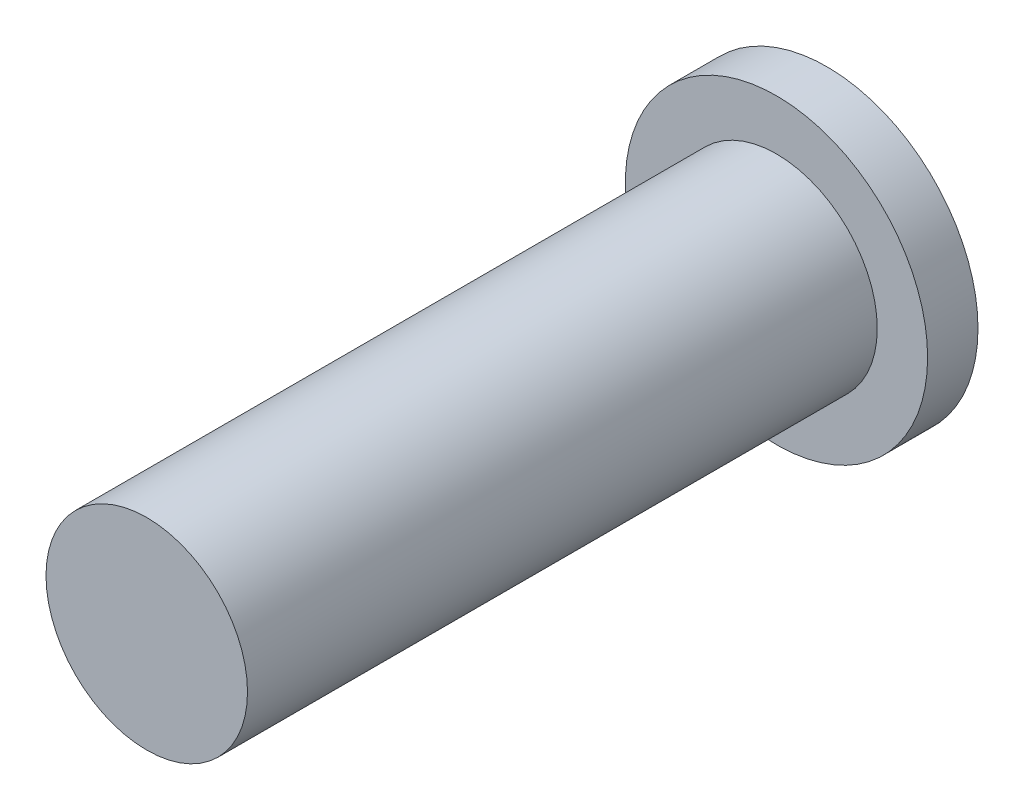
SolidWorks part; units mm, degrees
ref_plane "前视基准面" through (0, 0, 0) normal (0, 0, 1) x (1, 0, 0)
ref_plane "上视基准面" through (0, 0, 0) normal (0, 1, 0) x (1, 0, 0)
ref_plane "右视基准面" through (0, 0, 0) normal (1, 0, 0) x (0, 0, -1)
sketch "草图1" plane through (0, 0, 0) normal (0, 0, 1) x (1, 0, 0)
  circle A0 centre (0, 0) radius 6
  dimension "D1" = 12
extrude "凸台-拉伸1" add sketch "草图1" along normal blind 2
sketch "草图2" plane through (0, 0, 2) normal (0, 0, 1) x (1, 0, 0)
  circle A0 centre (0, 0) radius 4
  dimension "D1" = 8
extrude "凸台-拉伸2" add sketch "草图2" along normal blind 25
cosmetic thread "装饰螺纹线1" parameters "D1"=9, "D2"=6.647
